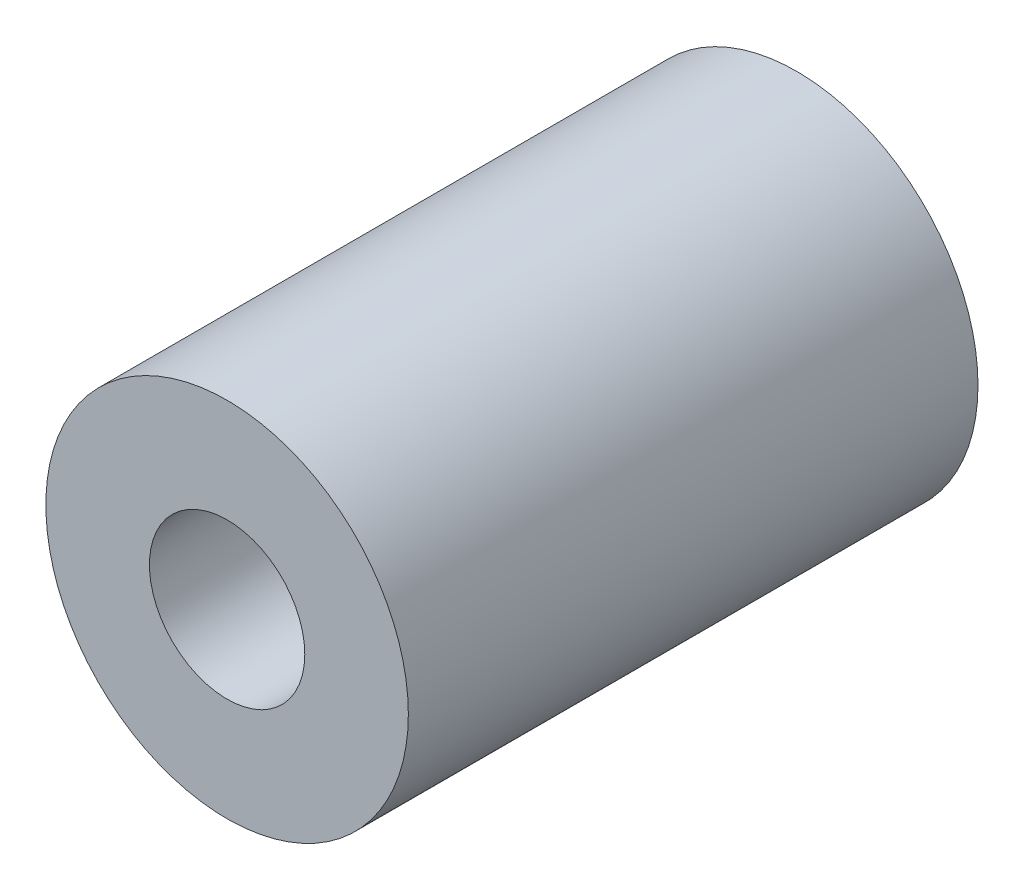
SolidWorks part; units mm, degrees
ref_plane "前视基准面" through (0, 0, 0) normal (0, 0, 1) x (1, 0, 0)
ref_plane "上视基准面" through (0, 0, 0) normal (0, 1, 0) x (1, 0, 0)
ref_plane "右视基准面" through (0, 0, 0) normal (1, 0, 0) x (0, 0, -1)
sketch "草图1" plane through (0, 0, 0) normal (0, 0, 1) x (1, 0, 0)
  circle A0 centre (0, 0) radius 7
  dimension "D1" = 14
extrude "凸台-拉伸1" add sketch "草图1" along normal blind 22
sketch "草图2" plane through (0, 0, 22) normal (0, 0, 1) x (1, 0, 0)
  circle A0 centre (0, 0) radius 3
  dimension "D1" = 6
extrude "切除-拉伸1" cut sketch "草图2" against normal through all
